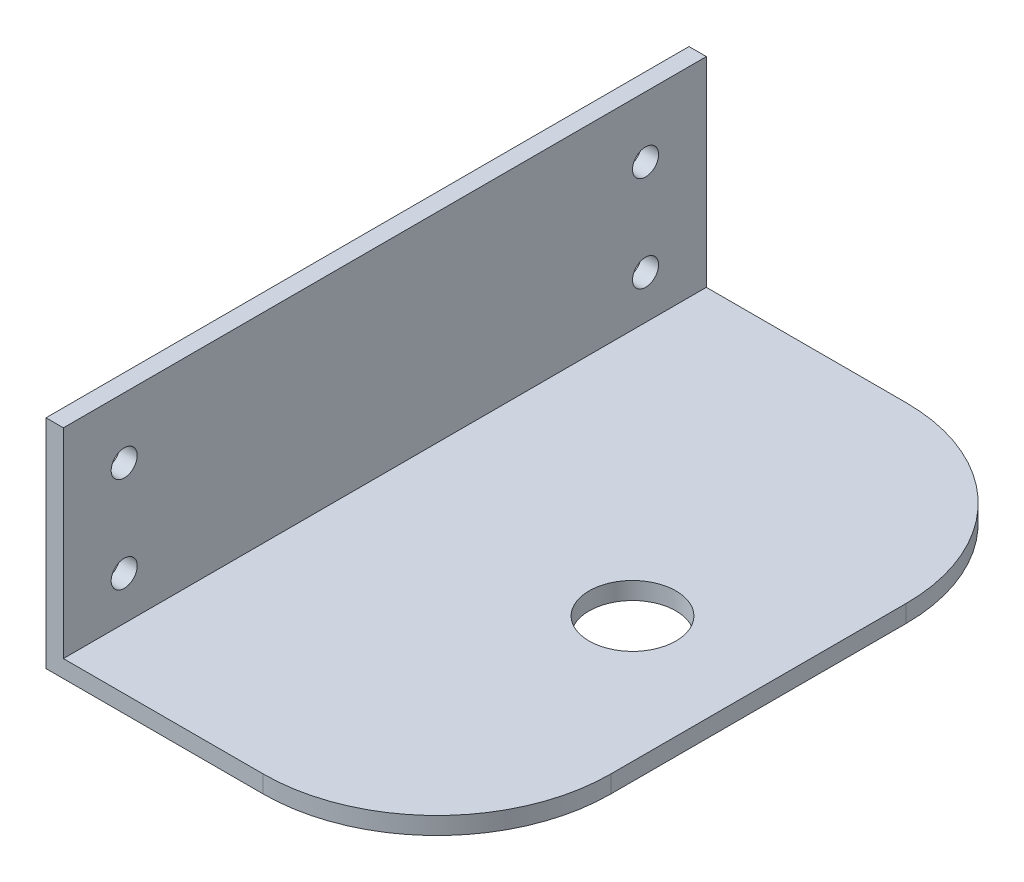
SolidWorks part; units mm, degrees
ref_plane "Front Plane" through (0, 0, 0) normal (0, 0, 1) x (1, 0, 0)
ref_plane "Top Plane" through (0, 0, 0) normal (0, 1, 0) x (1, 0, 0)
ref_plane "Right Plane" through (0, 0, 0) normal (1, 0, 0) x (0, 0, -1)
sketch "Sketch1" plane through (0, 0, 0) normal (0, 1, 0) x (1, 0, 0)
  line L0 (0, 0) -> (-30.5, 0) construction
  line L1 (-30.5, 37) -> (14.5, 37)
  line L2 (-30.5, 37) -> (-30.5, -37)
  line L3 (-30.5, -37) -> (14.5, -37)
  line L4 (14.5, 37) -> (14.5, -37)
  circle A0 centre (0, 0) radius 5
  dimension "D4" = 10
  dimension "D1" = 45
  dimension "D2" = 74
  dimension "D3" = 30.5
extrude "Boss-Extrude1" add sketch "Sketch1" along normal blind 2
sketch "Sketch2" plane through (0, 2, 0) normal (0, 1, 0) x (1, 0, 0)
  line L0 (-30.5, -37) -> (14.5, -37) construction
  line L1 (-30.5, 37) -> (-28.5, 37)
  line L2 (-30.5, 37) -> (-30.5, -37)
  line L3 (-30.5, -37) -> (-28.5, -37)
  line L4 (-28.5, 37) -> (-28.5, -37)
  dimension "D1" = 2
extrude "Boss-Extrude2" add sketch "Sketch2" along normal blind 23
sketch "Sketch3" plane through (-28.5, 0, 0) normal (1, 0, 0) x (0, 0, -1)
  line L0 (-37, 13.5) -> (-30, 13.5) construction
  line L1 (-37, 25) -> (-37, 2) construction
  line L2 (-30, 18) -> (-30, 7) construction
  line L3 (0, 25) -> (0, 12.5373) construction
  line L4 (-37, 25) -> (37, 25) construction
  circle A0 centre (-30, 18) radius 1.5
  circle A4 centre (-30, 7) radius 1.5
  circle A5 centre (30, 7) radius 1.5
  circle A6 centre (30, 18) radius 1.5
  point P7 (-30, 12.5)
  dimension "D2" = 3
  dimension "D4" = 18
  dimension "D1" = 7
  dimension "D3" = 7
extrude "Cut-Extrude1" cut sketch "Sketch3" against normal through all both and the other way through all
fillet "Fillet1" radius 20 2 edges at (14.5, 1, 37) (14.5, 1, -37)
